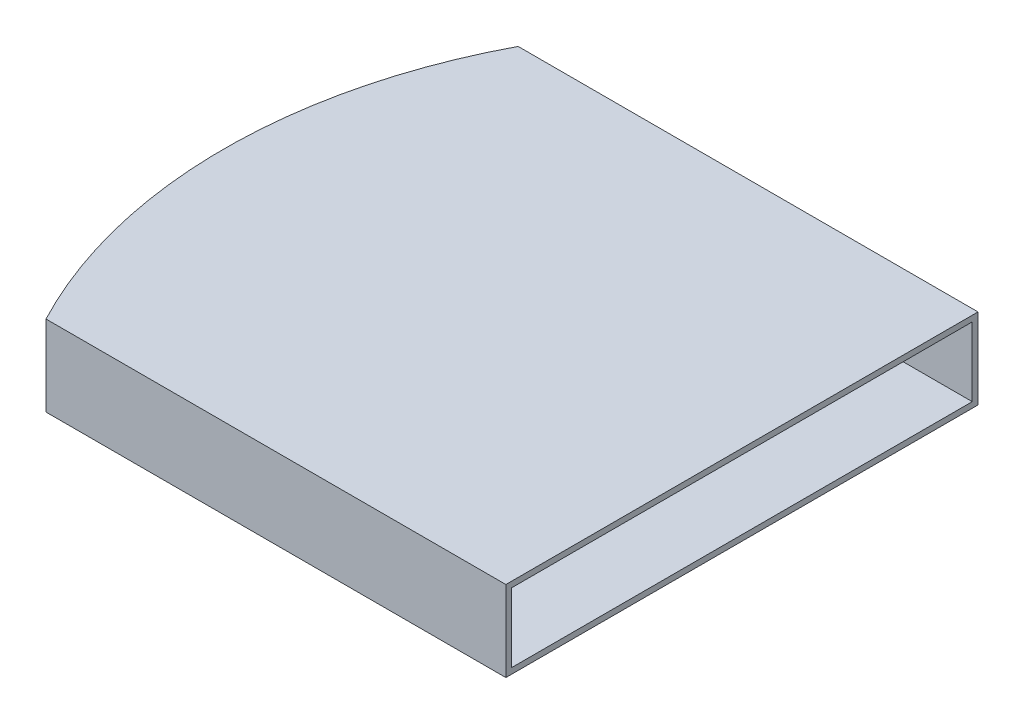
SolidWorks part; units mm, degrees
ref_plane "Front Plane" through (0, 0, 0) normal (0, 0, 1) x (1, 0, 0)
ref_plane "Top Plane" through (0, 0, 0) normal (0, 1, 0) x (1, 0, 0)
ref_plane "Right Plane" through (0, 0, 0) normal (1, 0, 0) x (0, 0, -1)
sketch "Sketch1" plane through (0, 0, 0) normal (0, 1, 0) x (1, 0, 0)
  line L1 (-253.5722, 260.35) -> (0, 260.35)
  line L3 (-253.5722, 0) -> (0, 0)
  line L4 (0, 260.35) -> (0, 0)
  line L5 (-253.5722, 260.35) -> (0, 0) construction
  line L6 (-253.5722, 0) -> (0, 260.35) construction
  arc A0 (-253.5722, 260.35) -> (-253.5722, 0) centre (-6.35, 130.175) ccw
  point P4 (-126.7861, 130.175)
  point P5 (-285.75, 130.175)
  dimension "D2" = 279.4
  dimension "D1" = 260.35
  dimension "D3" = 285.75
extrude "Boss-Extrude1" add sketch "Sketch1" along normal blind 44.45
ref_plane "Plane1" through (0, 0, -3.175) normal (0, 0, 1) x (1, 0, 0)
sketch "Sketch2" plane through (0, 0, -3.175) normal (0, 0, 1) x (1, 0, 0)
  line L0 (-247.2222, 41.275) -> (-215.2525, 3.175)
  line L1 (-247.2222, 41.275) -> (32.8376, 41.275)
  line L3 (-215.2525, 3.175) -> (32.8376, 3.175)
  line L4 (32.8376, 41.275) -> (32.8376, 3.175)
  line L5 (-253.5722, 44.45) -> (0, 44.45) construction
  line L7 (-253.5722, 44.45) -> (-253.5722, 0) construction
  dimension "D1" = 50
  dimension "D2" = 38.1
  dimension "D3" = 3.175
  dimension "D4" = 6.35
extrude "Cut-Extrude2" cut sketch "Sketch2" against normal blind 254
